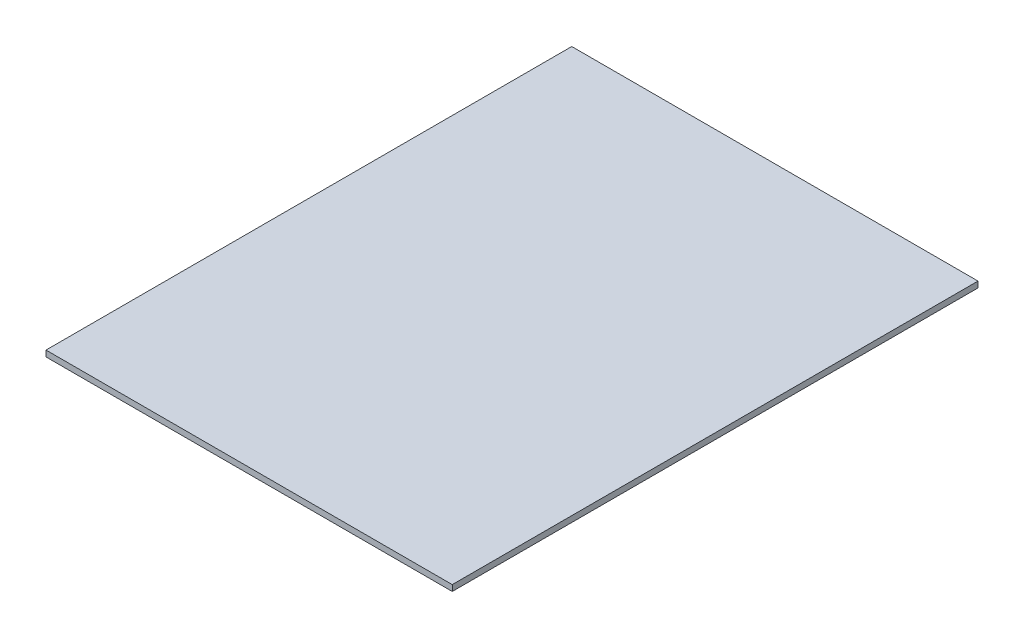
SolidWorks part; units mm, degrees
ref_plane "Front Plane" through (0, 0, 0) normal (0, 0, 1) x (1, 0, 0)
ref_plane "Top Plane" through (0, 0, 0) normal (0, 1, 0) x (1, 0, 0)
ref_plane "Right Plane" through (0, 0, 0) normal (1, 0, 0) x (0, 0, -1)
sketch "Sketch1" plane through (0, 0, 0) normal (0, 1, 0) x (1, 0, 0)
  line L0 (0, 0) -> (215.9, 0)
  line L1 (215.9, 0) -> (215.9, 279.4)
  line L2 (215.9, 279.4) -> (0, 279.4)
  line L3 (0, 279.4) -> (0, 0)
  dimension "D1" = 279.4
  dimension "D2" = 215.9
extrude "Boss-Extrude1" add sketch "Sketch1" along normal blind 3.175
